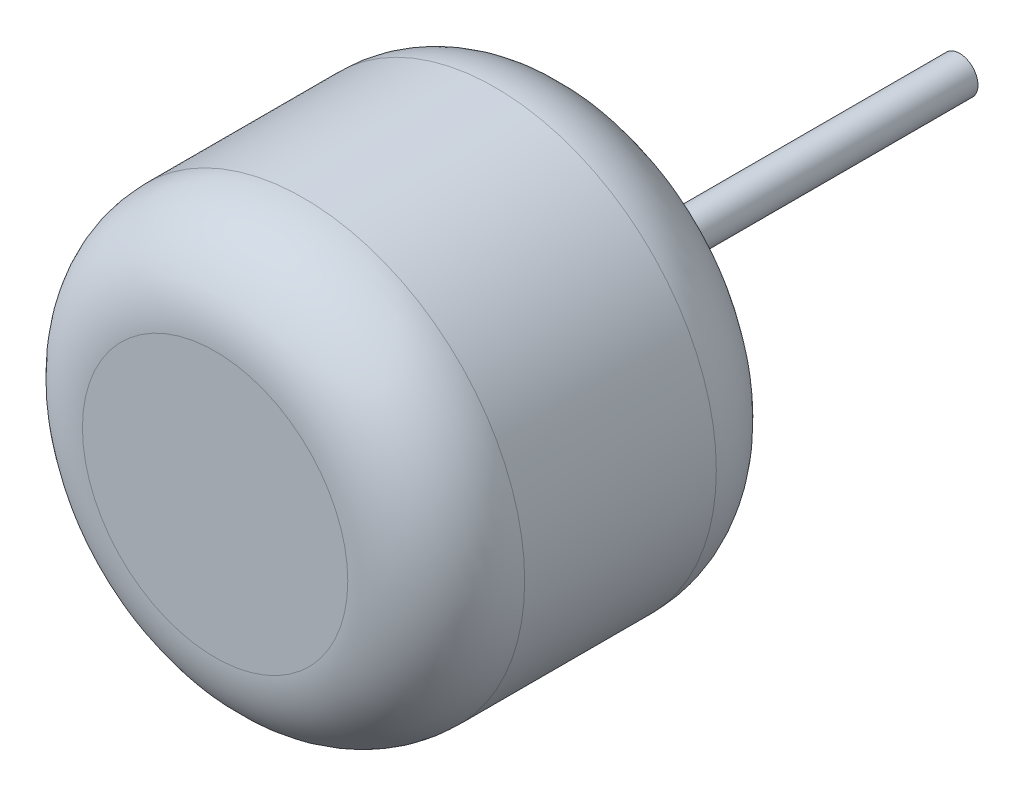
SolidWorks part; units mm, degrees
ref_plane "Front Plane" through (0, 0, 0) normal (0, 0, 1) x (1, 0, 0)
ref_plane "Top Plane" through (0, 0, 0) normal (0, 1, 0) x (1, 0, 0)
ref_plane "Right Plane" through (0, 0, 0) normal (1, 0, 0) x (0, 0, -1)
sketch "Sketch2" plane through (0, 0, 0) normal (0, 0, 1) x (1, 0, 0)
  circle A0 centre (0, 0) radius 150
  dimension "D1" = 300
extrude "Boss-Extrude1" add sketch "Sketch2" along normal blind 250
sketch "Sketch3" plane through (0, 0, 0) normal (0, 0, -1) x (-1, 0, 0)
  circle A0 centre (0, 0) radius 12.5
  dimension "D1" = 25
extrude "Boss-Extrude2" add sketch "Sketch3" along normal blind 255
fillet "Fillet1" radius 60 2 edges at (150, 0, 0) (150, 0, 250)
